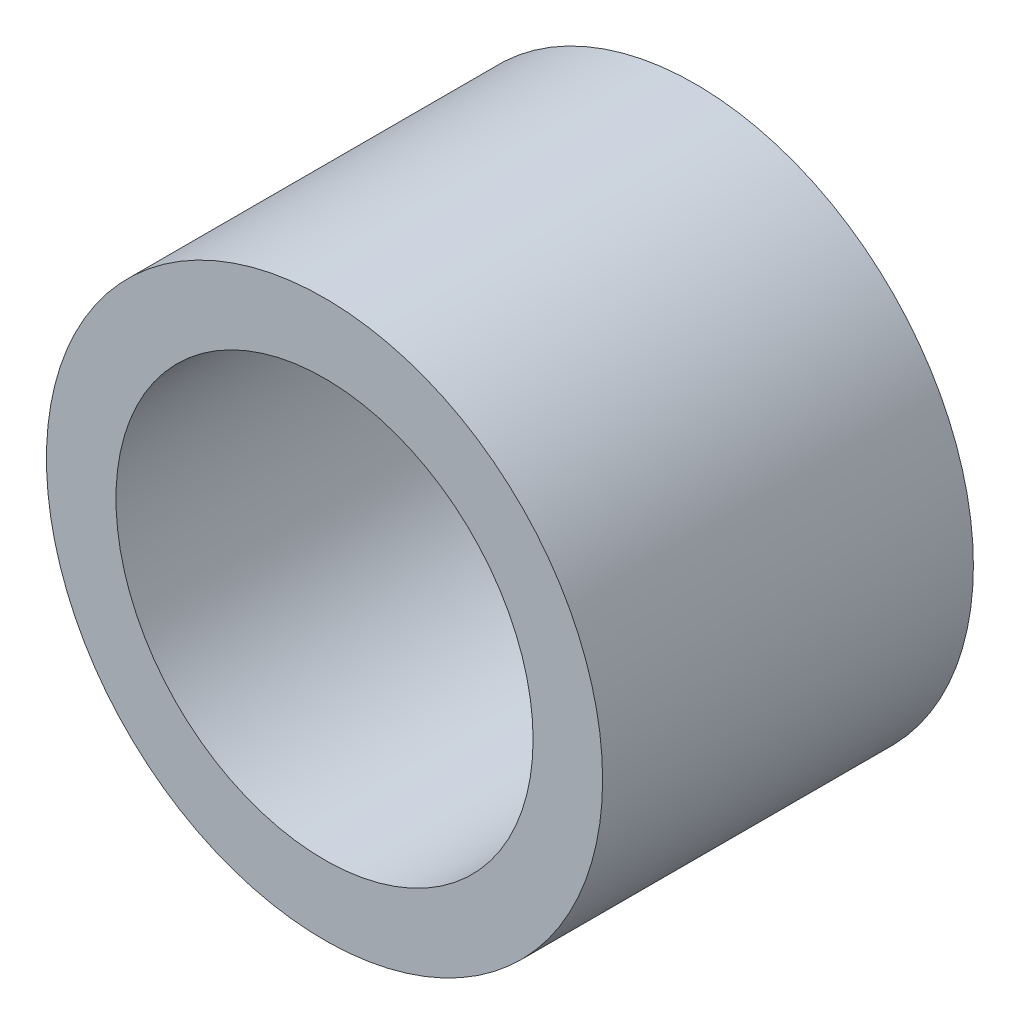
SolidWorks part; units mm, degrees
ref_plane "Plan de face" through (0, 0, 0) normal (0, 0, 1) x (1, 0, 0)
ref_plane "Plan de dessus" through (0, 0, 0) normal (0, 1, 0) x (1, 0, 0)
ref_plane "Plan de droite" through (0, 0, 0) normal (1, 0, 0) x (0, 0, -1)
sketch "Esquisse1" plane through (0, 0, 0) normal (0, 0, 1) x (1, 0, 0)
  circle A0 centre (0, 0) radius 6
  circle A1 centre (0, 0) radius 4.5
  dimension "D1" = 12
  dimension "D2" = 9
extrude "Boss.-Extru.1" add sketch "Esquisse1" along normal mid plane 8
